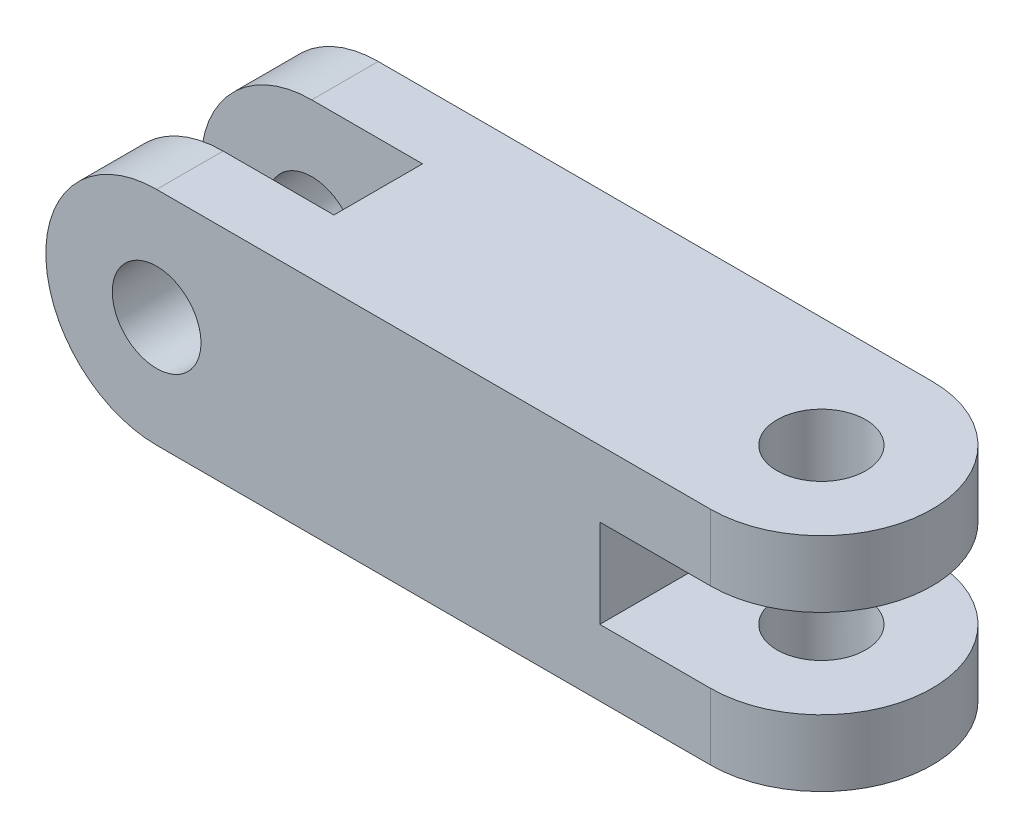
SolidWorks part; units mm, degrees
ref_plane "Front Plane" through (0, 0, 0) normal (0, 0, 1) x (1, 0, 0)
ref_plane "Top Plane" through (0, 0, 0) normal (0, 1, 0) x (1, 0, 0)
ref_plane "Right Plane" through (0, 0, 0) normal (1, 0, 0) x (0, 0, -1)
sketch "Sketch2" plane through (0, 0, 0) normal (0, 1, 0) x (1, 0, 0)
  line L1 (-60, 25) -> (65, 25)
  line L2 (-60, 25) -> (-60, -25)
  line L3 (-60, -25) -> (65, -25)
  arc A0 (65, -25) -> (65, 25) centre (65, 0) ccw
  point P0 (0, 0)
  dimension "D3" = 50
  dimension "D1" = 125
  dimension "D2" = 50
extrude "Boss-Extrude1" add sketch "Sketch2" along normal blind 50
sketch "Sketch3" plane through (0, 0, 25) normal (0, 0, 1) x (1, 0, 0)
  line L0 (-60, 50) -> (-60, 0) construction
  line L1 (-60, 50) -> (-60, 0)
  arc A0 (-60, 50) -> (-60, 0) centre (-60, 25) ccw
  dimension "D2" = 50
extrude "Boss-Extrude4" add sketch "Sketch3" against normal blind 50
sketch "Sketch5" plane through (0, 50, 0) normal (0, 1, 0) x (1, 0, 0)
  line L2 (-85, -10) -> (-35, -10)
  line L3 (-85, 10) -> (-35, 10)
  line L4 (-85, 10) -> (-85, -10)
  line L5 (-35, 10) -> (-35, -10)
extrude "Cut-Extrude2" cut sketch "Sketch5" against normal blind 50
sketch "Sketch6" plane through (0, 0, 25) normal (0, 0, 1) x (1, 0, 0)
  line L2 (90, 35) -> (40, 35)
  line L3 (90, 15) -> (40, 15)
  line L4 (40, 35) -> (40, 15)
  line L5 (90, 35) -> (90, 15)
extrude "Cut-Extrude3" cut sketch "Sketch6" against normal blind 50
sketch "Sketch7" plane through (0, 50, 0) normal (0, 1, 0) x (1, 0, 0)
  circle A0 centre (65, 0) radius 10
  dimension "D1" = 20
extrude "Cut-Extrude4" cut sketch "Sketch7" against normal blind 50
sketch "Sketch8" plane through (0, 0, -25) normal (0, 0, -1) x (-1, 0, 0)
  circle A0 centre (60, 25) radius 10
  dimension "D1" = 20
extrude "Cut-Extrude5" cut sketch "Sketch8" against normal blind 50
